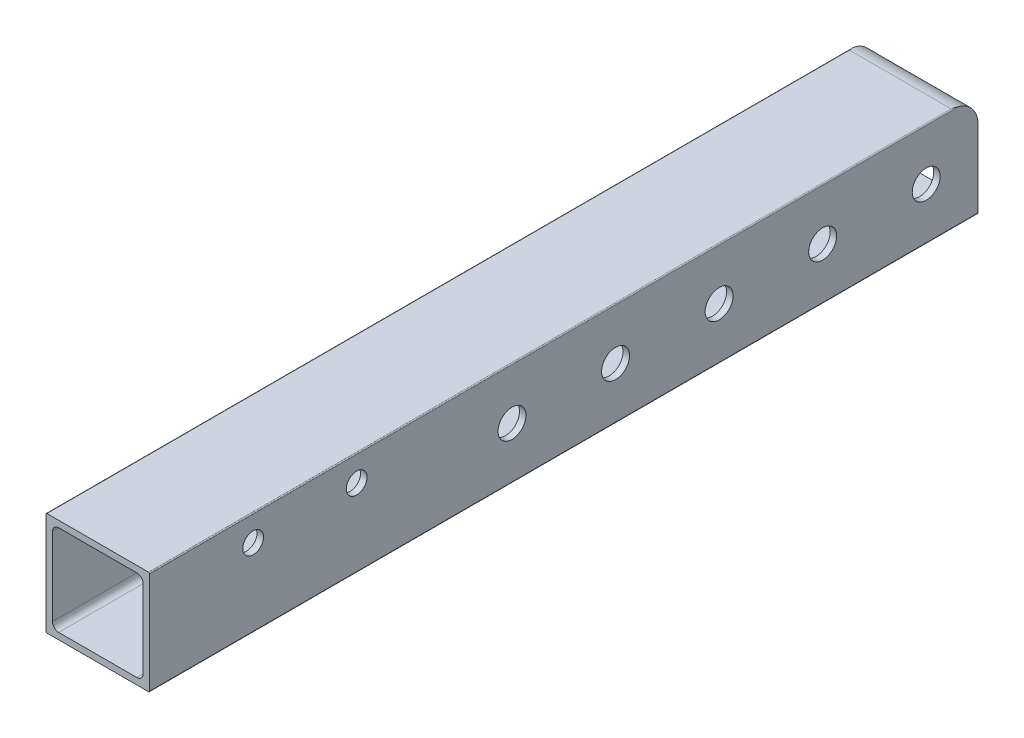
SolidWorks part; units mm, degrees
ref_plane "Front Plane" through (0, 0, 0) normal (0, 0, 1) x (1, 0, 0)
ref_plane "Top Plane" through (0, 0, 0) normal (0, 1, 0) x (1, 0, 0)
ref_plane "Right Plane" through (0, 0, 0) normal (1, 0, 0) x (0, 0, -1)
sketch "Sketch1" plane through (0, 0, 0) normal (0, 0, 1) x (1, 0, 0)
  line L0 (-9.5885, 11.1125) -> (9.5885, 11.1125)
  line L1 (-12.446, -12.7) -> (12.446, -12.7)
  line L2 (-12.7, -12.446) -> (-12.7, 12.446)
  line L3 (-12.446, 12.7) -> (12.446, 12.7)
  line L4 (12.7, -12.446) -> (12.7, 12.446)
  line L5 (-12.7, -12.7) -> (12.7, 12.7) construction
  line L6 (-12.7, 12.7) -> (12.7, -12.7) construction
  line L7 (11.1125, -9.5885) -> (11.1125, 9.5885)
  line L8 (-9.5885, -11.1125) -> (9.5885, -11.1125)
  line L9 (-11.1125, -9.5885) -> (-11.1125, 9.5885)
  line L10 (-12.7, -12.7) -> (12.7, -12.7) construction
  line L11 (-12.7, -12.7) -> (-12.7, 12.7) construction
  line L12 (12.7, -12.7) -> (12.7, 12.7) construction
  line L13 (-12.7, 12.7) -> (12.7, 12.7) construction
  line L14 (-11.1125, -11.1125) -> (11.1125, -11.1125) construction
  line L15 (-11.1125, -11.1125) -> (-11.1125, 11.1125) construction
  line L16 (11.1125, -11.1125) -> (11.1125, 11.1125) construction
  line L17 (-11.1125, 11.1125) -> (11.1125, 11.1125) construction
  arc A0 (-12.446, -12.7) -> (-12.7, -12.446) centre (-12.446, -12.446) cw
  arc A1 (12.446, -12.7) -> (12.7, -12.446) centre (12.446, -12.446) ccw
  arc A2 (12.446, 12.7) -> (12.7, 12.446) centre (12.446, 12.446) cw
  arc A3 (-12.7, 12.446) -> (-12.446, 12.7) centre (-12.446, 12.446) cw
  arc A4 (-9.5885, -11.1125) -> (-11.1125, -9.5885) centre (-9.5885, -9.5885) cw
  arc A5 (11.1125, -9.5885) -> (9.5885, -11.1125) centre (9.5885, -9.5885) cw
  arc A6 (9.5885, 11.1125) -> (11.1125, 9.5885) centre (9.5885, 9.5885) cw
  arc A7 (-9.5885, 11.1125) -> (-11.1125, 9.5885) centre (-9.5885, 9.5885) ccw
  point P0 (0, 0)
  dimension "D3" = 0.254
  dimension "D4" = 1.524
  dimension "D1" = 25.4
  dimension "D2" = 1.5875
extrude "Boss-Extrude1" add sketch "Sketch1" along normal blind 203.2
sketch "Sketch2" plane through (-12.7, 0, 0) normal (-1, 0, 0) x (0, 0, 1)
  line L0 (0, 0) -> (203.2, 0) construction
  line L1 (0, 12.446) -> (0, -12.446) construction
  line L2 (203.2, 12.446) -> (203.2, -12.446) construction
  line L3 (6.35, 12.7) -> (0, 12.7)
  line L4 (0, 12.7) -> (0, 6.35)
  line L6 (203.2, 12.7) -> (0, 12.7) construction
  circle A0 centre (12.7, 0) radius 3.429
  circle A1 centre (38.1, 0) radius 3.429
  circle A2 centre (63.5, 0) radius 3.429
  circle A3 centre (88.9, 0) radius 3.429
  circle A4 centre (114.3, 0) radius 3.429
  arc A5 (0, 6.35) -> (6.35, 12.7) centre (6.35, 6.35) cw
  circle A6 centre (177.8, 6.35) radius 2.54
  circle A7 centre (152.4, 6.35) radius 2.54
  point P26 (0, 0)
  point P27 (152.4, 0)
  point P28 (152.4, -3.8277)
  dimension "D1" = 6.858
  dimension "D2" = 12.7
  dimension "D5" = 6.35
  dimension "D8" = 5.08
  dimension "D9" = 25.4
  dimension "D10" = 25.4
  dimension "D11" = 6.35
  dimension "D4" = 25.4
  dimension "D6" = 6.35
  dimension "D7" = 6.35
  dimension "D3" = 5
extrude "Cut-Extrude1" cut sketch "Sketch2" against normal through all
